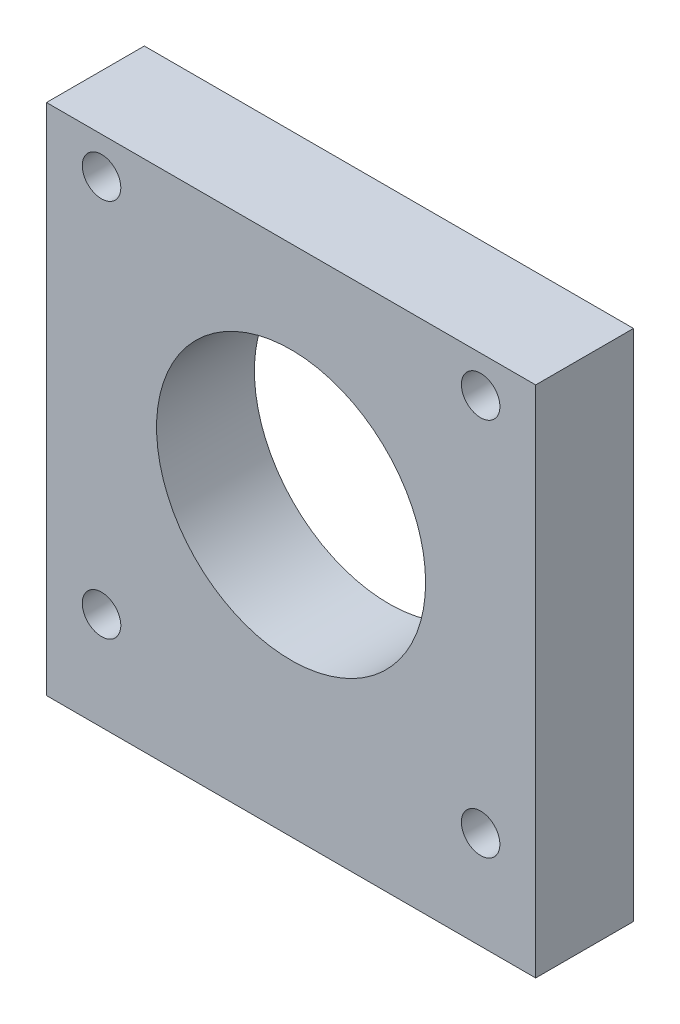
SolidWorks part; units mm, degrees
material "Liga 6061"
ref_plane "Plano frontal" through (0, 0, 0) normal (0, 0, 1) x (1, 0, 0)
ref_plane "Plano superior" through (0, 0, 0) normal (0, 1, 0) x (1, 0, 0)
ref_plane "Plano direito" through (0, 0, 0) normal (1, 0, 0) x (0, 0, -1)
sketch "Esboço1" plane through (0, 0, 0) normal (0, 0, 1) x (1, 0, 0)
  line L1 (20, -21) -> (-20, -21)
  line L2 (20, -21) -> (20, 21)
  line L3 (20, 21) -> (-20, 21)
  line L4 (-20, -21) -> (-20, 21)
  line L5 (20, -21) -> (-20, 21) construction
  line L6 (20, 21) -> (-20, -21) construction
  point P0 (0, 0)
  dimension "D1" = 42
  dimension "D2" = 40
extrude "Ressalto-extrusão1" add sketch "Esboço1" along normal blind 8
sketch "Esboço2" plane through (0, 0, 8) normal (0, 0, 1) x (1, 0, 0)
  line L0 (0, 21.191) -> (0, -23.0958) construction
  line L1 (-20, -21) -> (20, -21) construction
  circle A0 centre (0, 2.5) radius 11
  dimension "D1" = 22
  dimension "D2" = 23.5
extrude "Corte-extrusão1" cut sketch "Esboço2" against normal through all
hole_wizard "Furo roscado para conduíte de M3x0.51" positions "Esboço4" profile "Esboço5" tap size "M3x0.5" standard "Helicoil® Metric"
sketch "Esboço4" plane through (0, -21, 0) normal (0, -1, 0) x (-1, 0, 0)
  line L0 (-20, -8) -> (-20, 0) construction
  line L1 (20, 0) -> (-20, 0) construction
  line L2 (20, -8) -> (20, 0) construction
  point P0 (-12, -4)
  point P2 (12, -4)
  dimension "D1" = 8
  dimension "D2" = 4
  dimension "D3" = 8
  dimension "D4" = 4
sketch "Esboço5" plane through (12, -21, 4) normal (1, 0, 0) x (0, 0, -1)
  line L0 (0, 0) -> (0, 10.9464)
  line L1 (0, 10.9464) -> (1.575, 10)
  line L2 (1.575, 10) -> (1.575, 0.308)
  line L3 (1.575, 0.308) -> (1.883, 0)
  line L5 (1.883, 0) -> (0, 0)
  line L6 (-1.575, 0.308) -> (-1.883, 0) construction
  line L10 (0, 10.9464) -> (-1.575, 10) construction
  line L11 (0, -6.35) -> (0, 107.95) construction
  dimension "Tap Drill Dia." = 3.15
  dimension "Tap Drill Depth" = 10
  dimension "Near C'Sink Dia." = 3.766
  dimension "Near C'Sink Angle" = 90
  dimension "Drill Angle" = 118
cosmetic thread "Rosca de furo1"
cosmetic thread "Rosca de furo2"
hole_wizard "Furo roscado para conduíte de M3x0.52" positions "Esboço6" profile "Esboço7" tap size "M3x0.5" standard "Helicoil® Metric" end condition through all
sketch "Esboço6" plane through (0, 0, 0) normal (0, 0, -1) x (-1, 0, 0)
  circle A0 centre (0, 2.5) radius 11 construction
  point P0 (-15.5, 18)
  point P2 (15.5, 18)
  point P4 (-15.5, -13)
  point P6 (15.5, -13)
  dimension "D1" = 15.5
  dimension "D2" = 15.5
  dimension "D3" = 15.5
  dimension "D4" = 15.5
  dimension "D5" = 15.5
  dimension "D6" = 15.5
  dimension "D7" = 15.5
  dimension "D8" = 15.5
sketch "Esboço7" plane through (15.5, 18, 0) normal (1, 0, 0) x (0, 1, 0)
  line L0 (0, 0) -> (0, 8)
  line L1 (0, 8) -> (1.575, 8)
  line L2 (1.575, 8) -> (1.575, 0.308)
  line L3 (1.575, 0.308) -> (1.883, 0)
  line L5 (1.883, 0) -> (0, 0)
  line L6 (-1.575, 0.308) -> (-1.883, 0) construction
  line L11 (0, -6.35) -> (0, 107.95) construction
  dimension "Thru Tap Drill Dia." = 3.15
  dimension "Thru Tap Drill Depth" = 8
  dimension "Near C'Sink Dia." = 3.766
  dimension "Near C'Sink Angle" = 90
cosmetic thread "Rosca de furo3"
cosmetic thread "Rosca de furo4"
cosmetic thread "Rosca de furo5"
cosmetic thread "Rosca de furo6"
